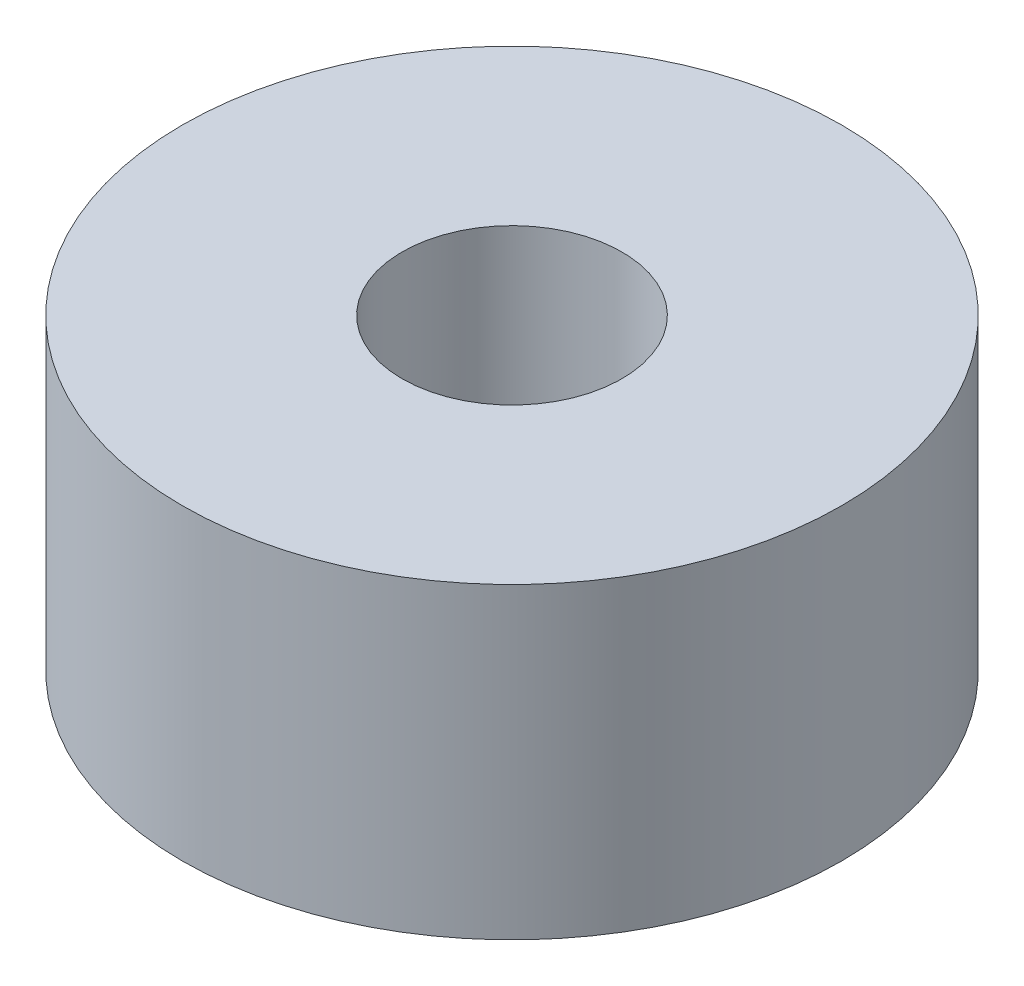
SolidWorks part; units mm, degrees
ref_plane "Płaszczyzna przednia" through (0, 0, 0) normal (0, 0, 1) x (1, 0, 0)
ref_plane "Płaszczyzna górna" through (0, 0, 0) normal (0, 1, 0) x (1, 0, 0)
ref_plane "Płaszczyzna prawa" through (0, 0, 0) normal (1, 0, 0) x (0, 0, -1)
sketch "Sketch1" plane through (0, 0, 0) normal (0, 1, 0) x (1, 0, 0)
  circle A0 centre (0, 0) radius 15
  circle A1 centre (0, 0) radius 5
  dimension "D1" = 10
  dimension "D2" = 30
extrude "Boss-Extrude1" add sketch "Sketch1" along normal blind 14
